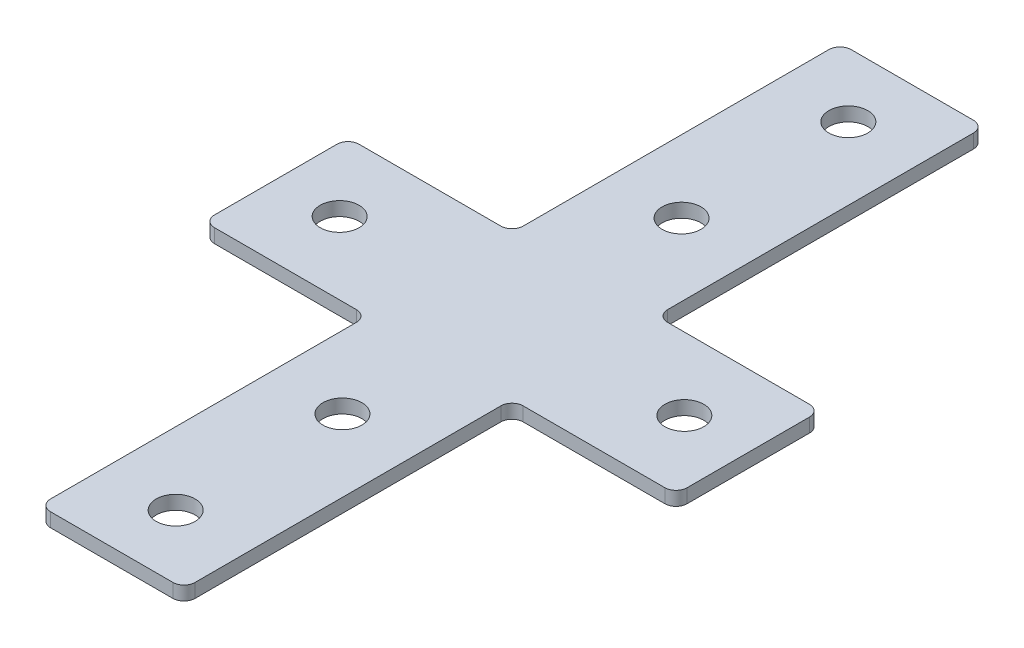
SolidWorks part; units mm, degrees
material "201 退火不锈钢 (SS)"
ref_plane "前视基准面" through (0, 0, 0) normal (0, 0, 1) x (1, 0, 0)
ref_plane "上视基准面" through (0, 0, 0) normal (0, 1, 0) x (1, 0, 0)
ref_plane "右视基准面" through (0, 0, 0) normal (1, 0, 0) x (0, 0, -1)
sketch "草图1" plane through (0, 0, 0) normal (0, 1, 0) x (1, 0, 0)
  line L0 (-42.5, 0) -> (-27.5, 0) construction
  line L5 (-13, 72) -> (13, 72)
  line L6 (-13, 72) -> (-13, 13)
  line L7 (-13, -72) -> (13, -72)
  line L8 (13, 72) -> (13, 13)
  line L11 (-42.5, 13) -> (-13, 13)
  line L12 (-42.5, 13) -> (-42.5, -13)
  line L13 (-42.5, -13) -> (-13, -13)
  line L14 (42.5, 13) -> (42.5, -13)
  line L19 (-13, -13) -> (-13, -72)
  line L23 (13, 13) -> (42.5, 13)
  line L24 (27.5, 0) -> (42.5, 0) construction
  line L25 (13, -13) -> (13, -72)
  line L26 (13, -13) -> (42.5, -13)
  circle A0 centre (0, -60.5) radius 3.5
  circle A1 centre (0, -30.5) radius 3.5
  circle A2 centre (-31, 0) radius 3.5
  circle A3 centre (31, 0) radius 3.5
  circle A4 centre (0, 60.5) radius 3.5
  circle A5 centre (0, 30.5) radius 3.5
  point P0 (0, 0)
  point P6 (0, 0)
  dimension "D5" = 7
  dimension "D6" = 7
  dimension "D7" = 30
  dimension "D8" = 11.5
  dimension "D9" = 7
  dimension "D10" = 7
  dimension "D11" = 11.5
  dimension "D12" = 11.5
  dimension "D1" = 26
  dimension "D2" = 144
  dimension "D3" = 26
  dimension "D4" = 85
extrude "凸台-拉伸1" add sketch "草图1" along normal blind 2.5
fillet "圆角1" radius 2 12 edges at (-13, 1.25, 13) (13, 1.25, 13) (13, 1.25, -13) (-13, 1.25, -13) (-42.5, 1.25, -13) (-42.5, 1.25, 13) (-13, 1.25, 72) (13, 1.25, 72) (42.5, 1.25, 13) (42.5, 1.25, -13) (13, 1.25, -72) (-13, 1.25, -72)
